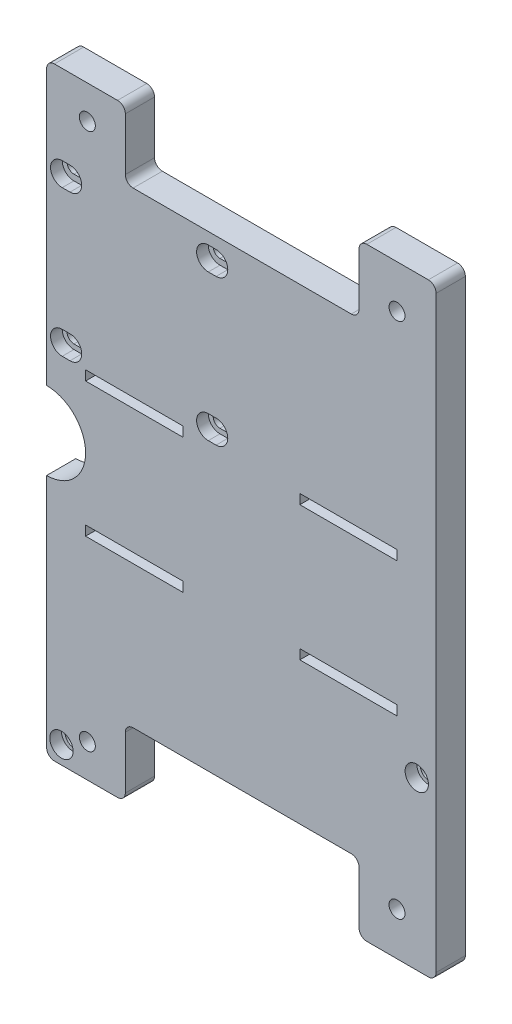
SolidWorks part; units mm, degrees
material "ABS"
ref_plane "Front Plane" through (0, 0, 0) normal (0, 0, 1) x (1, 0, 0)
ref_plane "Top Plane" through (0, 0, 0) normal (0, 1, 0) x (1, 0, 0)
ref_plane "Right Plane" through (0, 0, 0) normal (1, 0, 0) x (0, 0, -1)
sketch "Sketch1" plane through (0, 0, 0) normal (0, 0, 1) x (1, 0, 0)
  line L1 (0, 0) -> (100, 0)
  line L2 (0, 0) -> (0, 155)
  line L3 (0, 155) -> (100, 155)
  line L4 (100, 0) -> (100, 155)
  dimension "D1" = 100
  dimension "D2" = 155
extrude "Boss-Extrude1" add sketch "Sketch1" along normal blind 7.5
sketch "Sketch2" plane through (0, 0, 7.5) normal (0, 0, 1) x (1, 0, 0)
  line L0 (0, 77.5) -> (100, 77.5) construction
  line L1 (0, 155) -> (0, 0) construction
  line L2 (100, 0) -> (100, 155) construction
  line L3 (100, 155) -> (0, 155) construction
  line L4 (10.45, 146.45) -> (20.2, 146.45) construction
  line L5 (20.2, 137.5) -> (80.2, 137.5)
  line L6 (20.2, 137.5) -> (20.2, 155)
  line L7 (20.2, 155) -> (80.2, 155)
  line L8 (80.2, 137.5) -> (80.2, 155)
  line L9 (89.95, 143.95) -> (80.2, 143.95) construction
  line L10 (20.2, 0) -> (80.2, 0)
  line L11 (80.2, 17.5) -> (80.2, 0)
  line L12 (20.2, 17.5) -> (80.2, 17.5)
  line L13 (20.2, 17.5) -> (20.2, 0)
  circle A0 centre (10.45, 146.45) radius 2.05
  circle A1 centre (89.95, 143.95) radius 2.05
  circle A2 centre (89.95, 11.05) radius 2.05
  circle A3 centre (10.45, 8.55) radius 2.05
  dimension "D5" = 4.1
  dimension "D1" = 8.55
  dimension "D2" = 89.55
  dimension "D3" = 10.05
  dimension "D4" = 11.05
  dimension "D6" = 17.5
  dimension "D7" = 60
extrude "Hole cutouts" cut sketch "Sketch2" against normal through all
sketch "Sketch3" plane through (0, 0, 7.5) normal (0, 0, 1) x (1, 0, 0)
  line L0 (0, 72.5) -> (100, 72.5) construction
  line L1 (0, 155) -> (0, 0) construction
  line L2 (100, 0) -> (100, 155) construction
  line L3 (90, 56.5) -> (90, 54)
  line L4 (0, 56.5) -> (100, 56.5)
  line L5 (0, 56.5) -> (0, 88.5)
  line L6 (0, 88.5) -> (100, 88.5)
  line L7 (100, 56.5) -> (100, 88.5)
  line L8 (0, 56.5) -> (100, 88.5) construction
  line L9 (0, 88.5) -> (100, 56.5) construction
  line L10 (10, 88.5) -> (35, 88.5)
  line L11 (10, 88.5) -> (10, 91)
  line L12 (10, 91) -> (35, 91)
  line L13 (35, 88.5) -> (35, 91)
  line L14 (65, 88.5) -> (90, 88.5)
  line L15 (65, 88.5) -> (65, 91)
  line L16 (65, 91) -> (90, 91)
  line L17 (90, 88.5) -> (90, 91)
  line L18 (65, 54) -> (90, 54)
  line L19 (65, 56.5) -> (65, 54)
  line L20 (35, 56.5) -> (35, 54)
  line L21 (10, 56.5) -> (10, 54)
  line L22 (10, 54) -> (35, 54)
  line L23 (10, 56.5) -> (35, 56.5)
  line L24 (65, 56.5) -> (90, 56.5)
  point P6 (50, 72.5)
  point P27 (0, 77.5)
  dimension "D1" = 32
  dimension "D2" = 25
  dimension "D3" = 2.5
  dimension "D4" = 10
  dimension "D5" = 10
  dimension "D6" = 5
extrude "Battery strap holes" cut sketch "Sketch3" against normal through all contours L6 L13 L12 L11 | L6 L17 L16 L15 | L21 L22 L20 L4 | L4 L19 L18 L3
sketch "Sketch4" plane through (0, 0, 7.5) normal (0, 0, 1) x (1, 0, 0)
  line L0 (0, 112.88) -> (100, 112.88) construction
  line L1 (0, 155) -> (0, 0) construction
  line L2 (100, 0) -> (100, 155) construction
  line L5 (4, 131.76) -> (6, 131.76) construction
  line L7 (4, 133.51) -> (6, 133.51)
  line L8 (5, 94) -> (42.5, 94)
  line L9 (5, 94) -> (5, 131.76)
  line L10 (5, 131.76) -> (42.5, 131.76)
  line L11 (42.5, 94) -> (42.5, 131.76)
  line L12 (5, 94) -> (42.5, 131.76) construction
  line L13 (5, 131.76) -> (42.5, 94) construction
  line L14 (4, 130.01) -> (6, 130.01)
  line L15 (10, 91) -> (35, 91) construction
  line L16 (41.5, 131.76) -> (43.5, 131.76) construction
  line L17 (41.5, 133.51) -> (43.5, 133.51)
  line L18 (41.5, 130.01) -> (43.5, 130.01)
  line L19 (41.5, 94) -> (43.5, 94) construction
  line L20 (41.5, 92.25) -> (43.5, 92.25)
  line L21 (41.5, 95.75) -> (43.5, 95.75)
  line L22 (4, 94) -> (6, 94) construction
  line L23 (4, 92.25) -> (6, 92.25)
  line L24 (4, 95.75) -> (6, 95.75)
  arc A0 (4, 133.51) -> (4, 130.01) centre (4, 131.76) ccw
  arc A1 (6, 130.01) -> (6, 133.51) centre (6, 131.76) ccw
  arc A2 (41.5, 133.51) -> (41.5, 130.01) centre (41.5, 131.76) ccw
  arc A3 (43.5, 130.01) -> (43.5, 133.51) centre (43.5, 131.76) ccw
  arc A4 (41.5, 92.25) -> (41.5, 95.75) centre (41.5, 94) cw
  arc A5 (43.5, 95.75) -> (43.5, 92.25) centre (43.5, 94) cw
  arc A6 (4, 92.25) -> (4, 95.75) centre (4, 94) cw
  arc A7 (6, 95.75) -> (6, 92.25) centre (6, 94) cw
  point P8 (5, 131.76)
  point P10 (23.75, 112.88)
  point P18 (42.5, 131.76)
  point P30 (42.5, 94)
  point P37 (5, 94)
  dimension "D4" = 1.75
  dimension "D7" = 1.75
  dimension "D1" = 5
  dimension "D2" = 37.5
  dimension "D3" = 37.76
  dimension "D5" = 2
  dimension "D6" = 3
  dimension "D8" = 2
extrude "H-Bridge Holes" cut sketch "Sketch4" against normal blind 7.5 contours L10 A1 L7 A0 L14 L9 | L14 A1 L10 L9 | L10 A2 L18 L11 | L18 A3 L17 A2 L10 L11 | A7 L8 L9 L24 A6 L23 | A7 L24 L9 L8 | A5 L21 L11 L8 A4 L20 | A4 L8 L11 L21
fillet "Fillet1" radius 2 12 edges at (0, 0, 3.75) (20.2, 0, 3.75) (20.2, 17.5, 3.75) (80.2, 17.5, 3.75) (80.2, 0, 3.75) (100, 0, 3.75) (100, 155, 3.75) (80.2, 155, 3.75) (80.2, 137.5, 3.75) (20.2, 137.5, 3.75) (20.2, 155, 3.75) (0, 155, 3.75)
ref_plane "Plane1" through (50.2, 0, 0) normal (1, 0, 0) x (0, 0, -1)
sketch "Sketch9" plane through (0, 0, 7.5) normal (0, 0, 1) x (1, 0, 0)
  line L0 (0, 72.5) -> (100, 72.5) construction
  line L1 (0, 153) -> (0, 2) construction
  line L2 (100, 2) -> (100, 153) construction
  line L3 (22.5, 88.5) -> (22.5, 56.5) construction
  line L4 (10, 88.5) -> (35, 88.5) construction
  line L5 (10, 56.5) -> (35, 56.5) construction
  line L6 (0, 82.5) -> (0, 62.5)
  arc A0 (0, 82.5) -> (0, 62.5) centre (0, 72.5) cw
  point P12 (22.5, 72.5)
  dimension "D1" = 10
extrude "Camera Wire Hole" cut sketch "Sketch9" against normal through all
sketch "Sketch10" plane through (0, 0, 7.5) normal (0, 0, 1) x (1, 0, 0)
  line L0 (2, 0) -> (18.2, 0) construction
  line L1 (0, 62.5) -> (0, 2) construction
  line L2 (100, 2) -> (100, 153) construction
  line L3 (82.2, 0) -> (98, 0) construction
  circle A0 centre (3.8, 4.55) radius 2.05
  circle A1 centre (95.025, 42.825) radius 2.05
  dimension "D2" = 4.1
  dimension "D1" = 4.1
  dimension "D3" = 3.8
  dimension "D4" = 4.55
  dimension "D5" = 4.975
  dimension "D6" = 42.825
extrude "Cut-Extrude1" cut sketch "Sketch10" against normal up to surface (7.5 mm away) up to face at (46.6615, 77.1154, 0)
sketch "Sketch11" plane through (0, 0, 7.5) normal (0, 0, 1) x (1, 0, 0)
  line L0 (4, 94) -> (6, 94) construction
  line L1 (4, 97) -> (6, 97)
  line L2 (4, 91) -> (6, 91)
  line L3 (41.5, 91) -> (43.5, 91)
  line L4 (41.5, 97) -> (43.5, 97)
  line L5 (41.5, 94) -> (43.5, 94) construction
  line L6 (41.5, 128.5) -> (43.5, 128.5)
  line L7 (41.5, 134.5) -> (43.5, 134.5)
  line L8 (41.5, 131.5) -> (43.5, 131.5) construction
  line L9 (4, 128.5) -> (6, 128.5)
  line L10 (4, 134.5) -> (6, 134.5)
  line L11 (4, 131.5) -> (6, 131.5) construction
  circle A0 centre (3.8, 4.55) radius 3
  circle A1 centre (95.025, 42.825) radius 3
  arc A2 (4, 97) -> (4, 91) centre (4, 94) ccw
  arc A3 (6, 91) -> (6, 97) centre (6, 94) ccw
  arc A4 (41.5, 97) -> (41.5, 91) centre (41.5, 94) ccw
  arc A5 (43.5, 91) -> (43.5, 97) centre (43.5, 94) ccw
  arc A6 (41.5, 134.5) -> (41.5, 128.5) centre (41.5, 131.5) ccw
  arc A7 (43.5, 128.5) -> (43.5, 134.5) centre (43.5, 131.5) ccw
  arc A8 (4, 134.5) -> (4, 128.5) centre (4, 131.5) ccw
  arc A9 (6, 128.5) -> (6, 134.5) centre (6, 131.5) ccw
  point P10 (5, 94)
  point P19 (42.5, 94)
  point P26 (42.5, 131.5)
  point P33 (5, 131.5)
  dimension "D1" = 6
  dimension "D2" = 6
  dimension "D3" = 6
  dimension "D4" = 2
  dimension "D5" = 2
extrude "Cut-Extrude2" cut sketch "Sketch11" against normal blind 3
